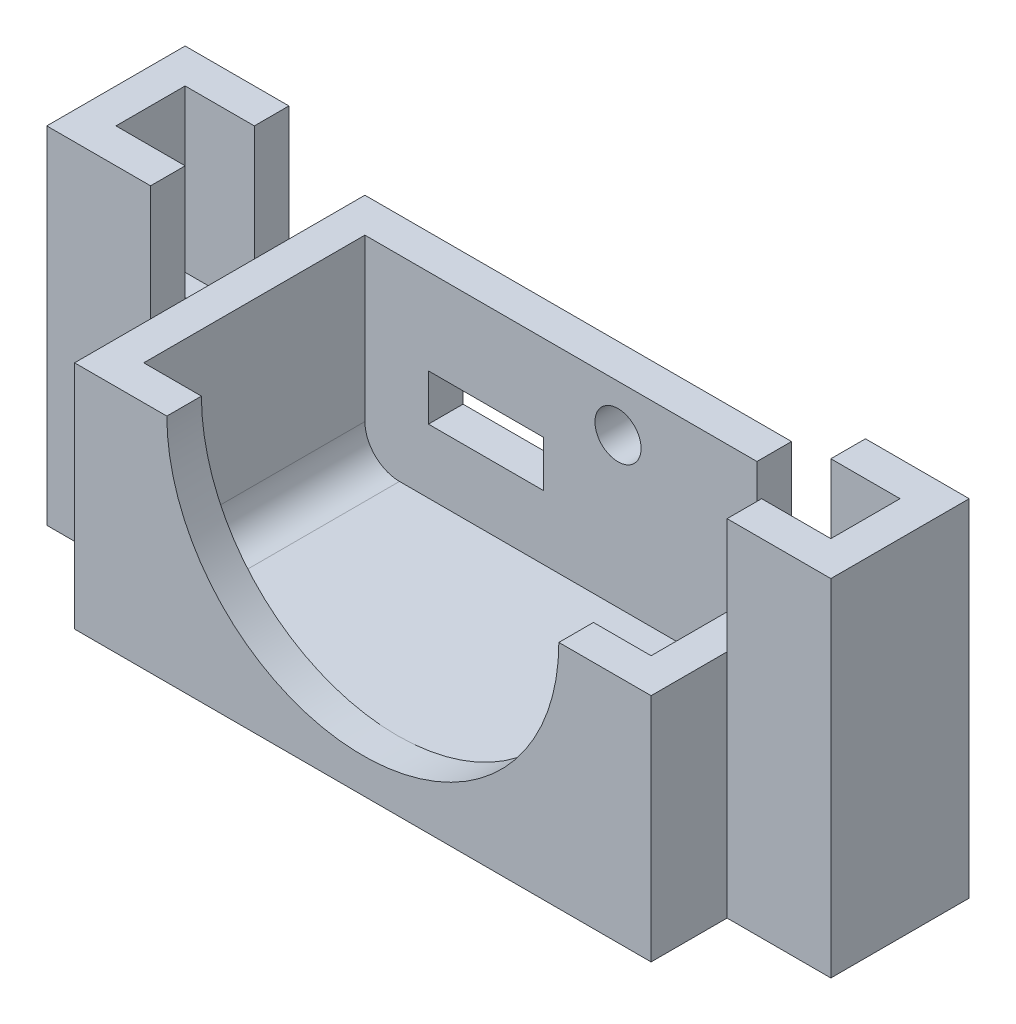
SolidWorks part; units mm, degrees
ref_plane "Front" through (0, 0, 0) normal (0, 0, 1) x (1, 0, 0)
ref_plane "Top" through (0, 0, 0) normal (0, 1, 0) x (1, 0, 0)
ref_plane "Right" through (0, 0, 0) normal (1, 0, 0) x (0, 0, -1)
sketch "Sketch1" plane through (0, 0, 0) normal (0, 1, 0) x (1, 0, 0)
  line L1 (-22, -9.59) -> (22, -9.59) construction
  line L2 (-22, -9.59) -> (-22, 9.59) construction
  line L3 (-22, 9.59) -> (22, 9.59) construction
  line L4 (22, -9.59) -> (22, 9.59) construction
  line L7 (-25, -12.59) -> (25, -12.59)
  line L8 (-25, -12.59) -> (-25, 12.59)
  line L9 (-25, 12.59) -> (25, 12.59)
  line L10 (25, -12.59) -> (25, 12.59)
  line L11 (-25, -12.59) -> (25, 12.59) construction
  line L12 (-25, 12.59) -> (25, -12.59) construction
  point P1 (0, 0)
  point P6 (0, 0)
  dimension "D1" = 44
  dimension "D2" = 19.18
  dimension "D3" = 50
  dimension "D4" = 25.18
extrude "Boss-Extrude1" add sketch "Sketch1" along normal blind 20
sketch "Sketch2" plane through (0, 20, 0) normal (0, 1, 0) x (1, 0, 0)
  line L1 (-22, -9.59) -> (22, -9.59)
  line L2 (-22, -9.59) -> (-22, 9.59)
  line L3 (-22, 9.59) -> (22, 9.59)
  line L4 (22, -9.59) -> (22, 9.59)
  line L5 (-22, -9.59) -> (22, 9.59) construction
  line L6 (-22, 9.59) -> (22, -9.59) construction
  point P0 (0, 0)
  dimension "D1" = 44
  dimension "D2" = 19.18
extrude "Cut-Extrude1" cut sketch "Sketch2" against normal blind 17
sketch "Sketch4" plane through (0, 0, 12.59) normal (0, 0, 1) x (1, 0, 0)
  line L0 (-25, 20) -> (-25, 0) construction
  line L1 (-25, 20) -> (25, 20) construction
  line L2 (-17, 20) -> (17, 20)
  line L3 (-22, 20) -> (22, 20) construction
  line L4 (-22, 20) -> (-22, 3) construction
  line L5 (-22, 3) -> (22, 3) construction
  line L6 (22, 20) -> (22, 3) construction
  arc A0 (-17, 20) -> (17, 20) centre (0, 20) ccw
  point P0 (-25, 10)
  point P1 (0, 20)
  dimension "D3" = 34
  dimension "D1" = 3
  dimension "D2" = 44
  dimension "19.18" = 17
  dimension "D4" = 0
extrude "Cut-Extrude2" cut sketch "Sketch4" against normal up to surface (3 mm away) up to face at (0, 11.5, 9.59)
sketch "Sketch5" plane through (0, 0, -12.59) normal (0, 0, -1) x (-1, 0, 0)
  line L0 (-25, 20) -> (-25, 0) construction
  line L1 (-22, 20) -> (22, 20) construction
  line L2 (-22, 20) -> (-22, 3) construction
  line L3 (-22, 3) -> (22, 3) construction
  line L4 (22, 20) -> (22, 3) construction
  line L5 (-49.2755, 32.4193) -> (-49.694, 32.4193)
  line L6 (-49.2755, 32.4193) -> (-49.2755, 33.7107)
  line L7 (-49.2755, 33.7107) -> (-49.694, 33.7107)
  line L8 (-49.694, 32.4193) -> (-49.694, 33.7107)
  line L9 (-25, 20) -> (25, 20) construction
  line L11 (-22, 20) -> (-12, 20)
  line L12 (-22, 20) -> (-22, 14)
  line L13 (-22, 14) -> (-12, 14)
  line L14 (-12, 20) -> (-12, 14)
  line L15 (6.49, 8.56) -> (16.49, 8.56)
  line L16 (6.49, 8.56) -> (6.49, 12.56)
  line L17 (6.49, 12.56) -> (16.49, 12.56)
  line L18 (16.49, 8.56) -> (16.49, 12.56)
  line L19 (6.49, 8.56) -> (16.49, 12.56) construction
  line L20 (6.49, 12.56) -> (16.49, 8.56) construction
  circle A0 centre (0.05, 15.95) radius 2
  point P13 (-22, 20)
  point P18 (11.49, 10.56)
  point P19 (11.49, 10.56)
  dimension "D9" = 4
  dimension "D1" = 3
  dimension "D2" = 0
  dimension "D3" = 44
  dimension "D4" = 17
  dimension "D5" = 10
  dimension "D6" = 6
  dimension "D7" = 22.05
  dimension "D8" = 12.95
  dimension "D10" = 7.56
  dimension "D11" = 33.49
  dimension "D12" = 10
  dimension "D13" = 4
extrude "Cut-Extrude3" cut sketch "Sketch5" against normal up to surface (3 mm away) up to face at (0, 11.5, -9.59)
fillet "Fillet1" radius 3 2 edges at (-22, 3, 0) (22, 3, 0)
sketch "Sketch7" plane through (0, 0, 0) normal (0, -1, 0) x (1, 0, 0)
  line L0 (-25, -12.59) -> (-25, 12.59) construction
  line L1 (0, 0) -> (0, 7.2563) construction
  line L2 (-25, 3) -> (-31, 3)
  line L3 (-25, 3) -> (-25, -3)
  line L4 (-25, -3) -> (-31, -3)
  line L5 (-31, 3) -> (-31, -3)
  line L6 (31, 3) -> (31, -3)
  line L7 (25, -3) -> (31, -3)
  line L8 (25, 3) -> (25, -3)
  line L9 (25, 3) -> (31, 3)
  circle A0 centre (-28, 0) radius 1.5
  circle A1 centre (28, 0) radius 1.5
  point P0 (-25, 0)
  point P1 (-25, 3)
  point P8 (-28, -3)
  point P9 (-31, 0)
  point P21 (31, 0)
  point P22 (28, -3)
  point P23 (25, 0)
  dimension "D4" = 3
  dimension "D1" = 3
  dimension "D2" = 6
  dimension "D3" = 6
extrude "Boss-Extrude2" add sketch "Sketch7" against normal blind 16
sketch "Sketch8" plane through (0, 0, 0) normal (0, -1, 0) x (1, 0, 0)
  line L1 (-25, -6) -> (-34, -6)
  line L2 (-25, -6) -> (-25, -3)
  line L3 (-25, 6) -> (-34, 6)
  line L4 (-34, -6) -> (-34, 6)
  line L5 (-25, -3) -> (-34, 6) construction
  line L6 (-25, 3) -> (-34, -6) construction
  line L7 (-25, -3) -> (-31, -3)
  line L9 (0, 0) -> (0, 9.238) construction
  line L10 (-25, 3) -> (-25, 6) construction
  line L11 (-31, -3) -> (-31, 3)
  line L12 (-31, 3) -> (-25, 3)
  line L13 (-25, -6) -> (-25, -3) construction
  line L14 (-25, 6) -> (-25.0323, 5.783)
  line L15 (-25, 3) -> (-25, 6)
  line L16 (-25, 3) -> (-25, 6) construction
  line L17 (25, 3) -> (25, 6) construction
  line L18 (25, -6) -> (25, -3) construction
  line L19 (25, 3) -> (25, 6) construction
  line L20 (25, 3) -> (34, -6) construction
  line L21 (25, -3) -> (34, 6) construction
  line L22 (25, 3) -> (25, 6)
  line L23 (25, 6) -> (25.0323, 5.783)
  line L24 (31, 3) -> (25, 3)
  line L25 (31, -3) -> (31, 3)
  line L26 (25, -3) -> (31, -3)
  line L27 (34, -6) -> (34, 6)
  line L28 (25, 6) -> (34, 6)
  line L29 (25, -6) -> (25, -3)
  line L30 (25, -6) -> (34, -6)
  point P0 (-28, 0)
  point P17 (-16.6525, 10.4231)
  point P18 (-19.2851, 19.7257)
  point P33 (19.2851, 19.7257)
  point P34 (16.6525, 10.4231)
  point P35 (28, 0)
  dimension "D1" = 3
extrude "Boss-Extrude3" add sketch "Sketch8" against normal blind 30
